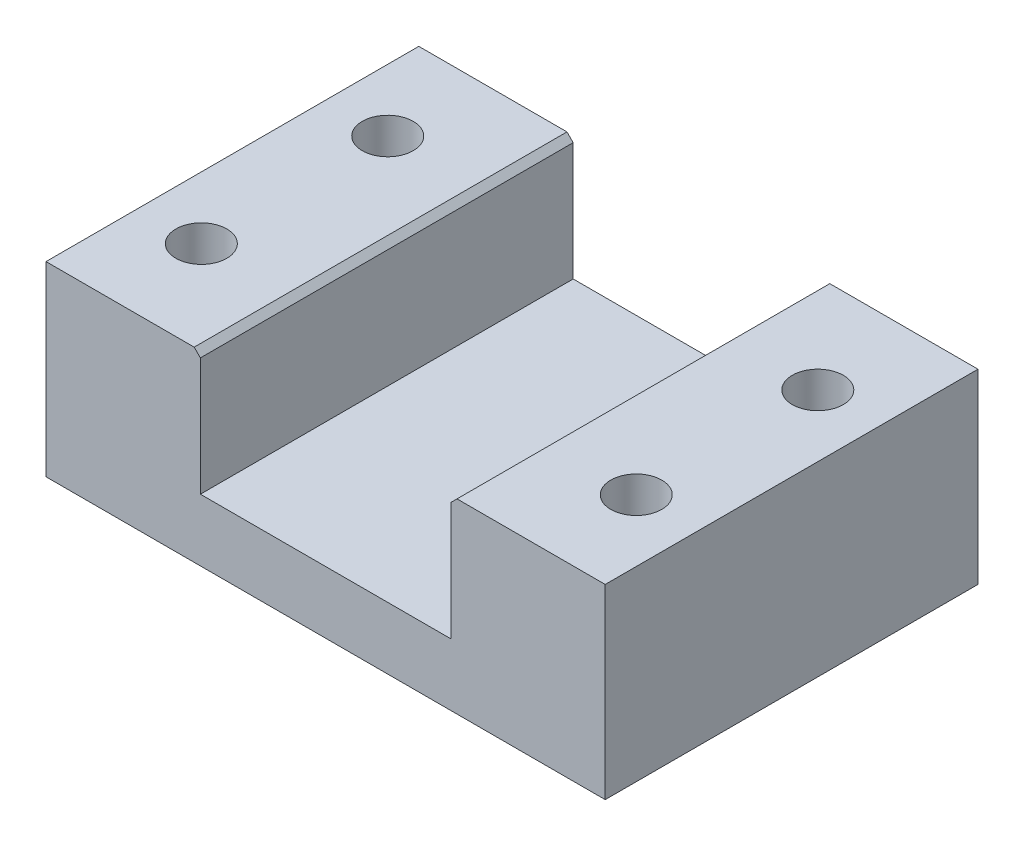
SolidWorks part; units mm, degrees
ref_plane "Спереди" through (0, 0, 0) normal (0, 0, 1) x (1, 0, 0)
ref_plane "Сверху" through (0, 0, 0) normal (0, 1, 0) x (1, 0, 0)
ref_plane "Справа" through (0, 0, 0) normal (1, 0, 0) x (0, 0, -1)
sketch "Sketch1" plane through (0, 0, 0) normal (0, 1, 0) x (1, 0, 0)
  line L1 (45, -30) -> (-45, -30)
  line L2 (45, -30) -> (45, 30)
  line L3 (45, 30) -> (-45, 30)
  line L4 (-45, -30) -> (-45, 30)
  line L5 (45, -30) -> (-45, 30) construction
  line L6 (45, 30) -> (-45, -30) construction
  point P0 (0, 0)
  dimension "D1" = 90
  dimension "D2" = 60
extrude "Boss-Extrude1" add sketch "Sketch1" along normal blind 30
sketch "Sketch2" plane through (0, 0, 30) normal (0, 0, 1) x (1, 0, 0)
  line L0 (-45, 30) -> (45, 30) construction
  line L1 (20.15, 50) -> (-20.15, 50)
  line L2 (20.15, 50) -> (20.15, 10)
  line L3 (20.15, 10) -> (-20.15, 10)
  line L4 (-20.15, 50) -> (-20.15, 10)
  line L5 (20.15, 50) -> (-20.15, 10) construction
  line L6 (20.15, 10) -> (-20.15, 50) construction
  point P0 (0, 30)
  dimension "D1" = 40.3
  dimension "D2" = 40
extrude "Cut-Extrude1" cut sketch "Sketch2" against normal through all
sketch "Sketch3" plane through (0, 0, 0) normal (0, -1, 0) x (1, 0, 0)
  line L1 (-35, -15) -> (35, -15) construction
  line L2 (-35, -15) -> (-35, 15) construction
  line L3 (-35, 15) -> (35, 15) construction
  line L4 (35, -15) -> (35, 15) construction
  line L5 (-35, -15) -> (35, 15) construction
  line L6 (-35, 15) -> (35, -15) construction
  circle A0 centre (-35, 15) radius 4.1
  circle A1 centre (-35, -15) radius 4.1
  circle A2 centre (35, -14.2173) radius 4.1
  circle A3 centre (35, 15) radius 4.1
  point P0 (0, 0)
  dimension "D3" = 8.2
  dimension "D1" = 30
  dimension "D2" = 70
extrude "Cut-Extrude2" cut sketch "Sketch3" against normal through all
sketch "Sketch4" plane through (0, 0, 0) normal (0, -1, 0) x (1, 0, 0)
  circle A0 centre (35, 15) radius 8.8
  circle A1 centre (35, -14.2173) radius 8.8
  circle A2 centre (-35, 15) radius 8.8
  circle A3 centre (-35, -15) radius 8.8
  dimension "D1" = 17.6
extrude "Cut-Extrude3" cut sketch "Sketch4" against normal blind 10
chamfer "Chamfer1" distance 1 angle 45 2 edges at (-20.15, 30, 0) (20.15, 30, 0)
